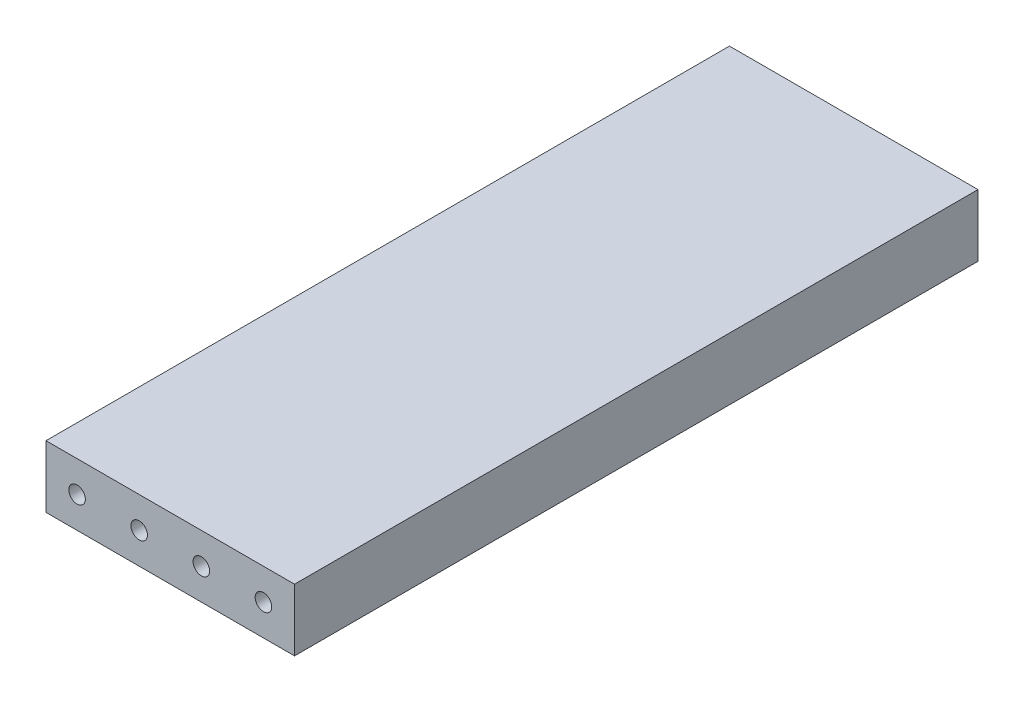
SolidWorks part; units mm, degrees
ref_plane "Front Plane" through (0, 0, 0) normal (0, 0, 1) x (1, 0, 0)
ref_plane "Top Plane" through (0, 0, 0) normal (0, 1, 0) x (1, 0, 0)
ref_plane "Right Plane" through (0, 0, 0) normal (1, 0, 0) x (0, 0, -1)
sketch "Sketch1" plane through (0, 0, 0) normal (0, 0, 1) x (1, 0, 0)
  line L1 (-60, -15) -> (60, -15)
  line L2 (-60, -15) -> (-60, 15)
  line L3 (-60, 15) -> (60, 15)
  line L4 (60, -15) -> (60, 15)
  line L5 (-60, -15) -> (60, 15) construction
  line L6 (-60, 15) -> (60, -15) construction
  point P0 (0, 0)
  dimension "D1" = 120
  dimension "D2" = 30
extrude "Boss-Extrude1" add sketch "Sketch1" along normal mid plane 330
sketch "Sketch2" plane through (0, 0, -165) normal (0, 0, -1) x (-1, 0, 0)
  line L0 (-60, 0) -> (60, 0) construction
  line L1 (-60, -15) -> (-60, 15) construction
  line L2 (60, 15) -> (60, -15) construction
  circle A0 centre (-45, 0) radius 4
  circle A1 centre (-15, 0) radius 4
  circle A2 centre (15, 0) radius 4
  circle A3 centre (45, 0) radius 4
  dimension "D3" = 75
  dimension "D4" = 8
  dimension "D5" = 8
  dimension "D6" = 8
  dimension "D7" = 105
  dimension "D8" = 8
  dimension "D1" = 15
  dimension "D2" = 45
extrude "Cut-Extrude1" cut sketch "Sketch2" against normal through all
